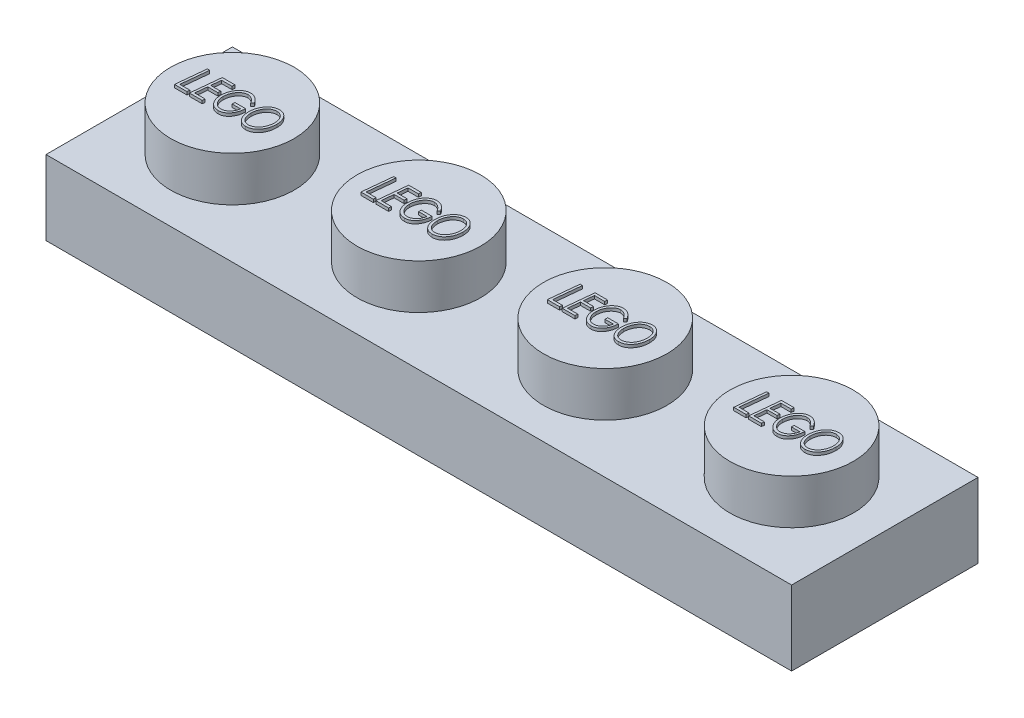
SolidWorks part; units mm, degrees
ref_plane "Front Plane" through (0, 0, 0) normal (0, 0, 1) x (1, 0, 0)
ref_plane "Top Plane" through (0, 0, 0) normal (0, 1, 0) x (1, 0, 0)
ref_plane "Right Plane" through (0, 0, 0) normal (1, 0, 0) x (0, 0, -1)
sketch "Sketch2" plane through (0, 0, 0) normal (0, 1, 0) x (1, 0, 0)
  line L0 (-17.7331, 8.7234) -> (14.0169, 8.7234)
  line L1 (14.0169, 8.7234) -> (14.0169, 0.7859)
  line L2 (14.0169, 0.7859) -> (-17.7331, 0.7859)
  line L3 (-17.7331, 0.7859) -> (-17.7331, 8.7234)
  point P4 (0, 0)
  dimension "D1" = 31.75
  dimension "D2" = 7.9375
extrude "Boss-Extrude3" add sketch "Sketch2" along normal blind 3.175
sketch "Sketch3" plane through (0, 3.175, 0) normal (0, 1, 0) x (1, 0, 0)
  line L0 (-17.7331, 8.7234) -> (-17.7331, 0.7859) construction
  line L1 (14.0169, 8.7234) -> (-17.7331, 8.7234) construction
  circle A0 centre (-13.7644, 4.7546) radius 2.6308
  dimension "D1" = 3.9687
  dimension "D2" = 3.9688
extrude "Boss-Extrude4" add sketch "Sketch3" along normal blind 1.905
pattern_linear "LPattern1" count 4 spacing 7.9375 along (1, 0, 0) of "Boss-Extrude4"
shell "Shell1" thickness 1.524
sketch "Sketch4" plane through (0, 5.08, 0) normal (0, 1, 0) x (1, 0, 0)
  line L1 (-13.7644, 4.7546) -> (-13.7644, 4.0766) construction
  line L2 (-15.584, 4.0766) -> (-11.9447, 4.0766) construction
  text T0 "<i>LEGO</i>" font "Century Gothic" height 1.27
  point P4 (-13.7644, 4.7546)
  point P9 (-13.7644, 4.0766)
extrude "Boss-Extrude5" add sketch "Sketch4" along normal blind 0.127
pattern_linear "LPattern2" count 4 spacing 7.9375 along (1, 0, 0) of "Boss-Extrude5"
sketch "Sketch5" plane through (0, 0, 0) normal (0, -1, 0) x (1, 0, 0)
  circle A0 centre (-9.7956, -4.7546) radius 1.4986
  circle A1 centre (-9.7956, -4.7546) radius 0.635
  dimension "D1" = 2.9972
  dimension "D2" = 1.27
extrude "Boss-Extrude6" add sketch "Sketch5" against normal up to surface (1.651 mm away) up to face at (-5.8269, 1.651, -5.8614)
pattern_linear "LPattern3" count 3 spacing 7.9375 along (1, 0, 0) of "Boss-Extrude6"
